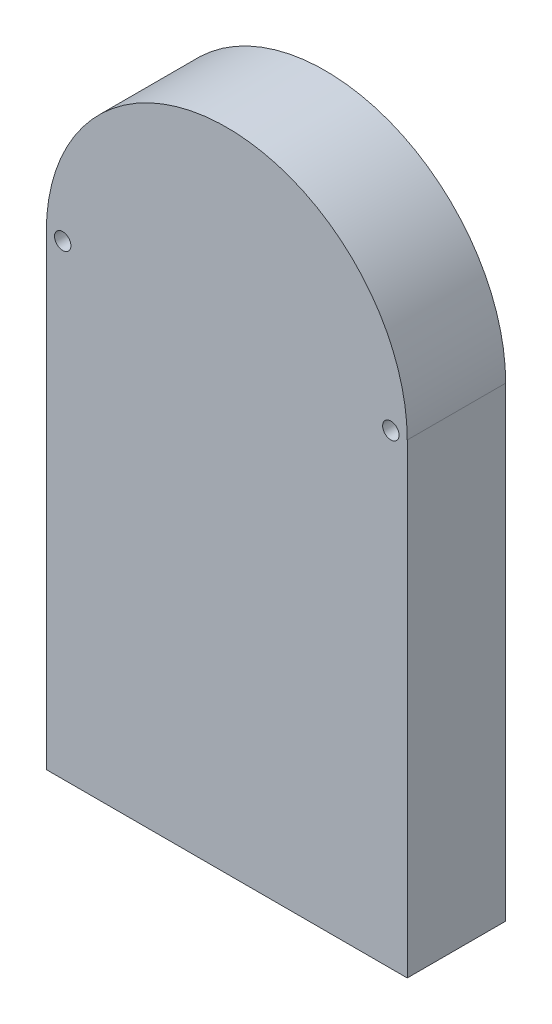
SolidWorks part; units mm, degrees
ref_plane "Front Plane" through (0, 0, 0) normal (0, 0, 1) x (1, 0, 0)
ref_plane "Top Plane" through (0, 0, 0) normal (0, 1, 0) x (1, 0, 0)
ref_plane "Right Plane" through (0, 0, 0) normal (1, 0, 0) x (0, 0, -1)
sketch "Sketch1" plane through (0, 0, 0) normal (0, 0, 1) x (1, 0, 0)
  line L0 (-57.2515, 0) -> (52.7485, 0)
  line L1 (52.7485, 0) -> (52.7485, 142)
  line L2 (-57.2515, 0) -> (-57.2515, 142)
  arc A0 (-57.2515, 142) -> (52.7485, 142) centre (-2.2515, 142) cw
  dimension "D1" = 110
  dimension "D2" = 142
  dimension "D3" = 142
extrude "Boss-Extrude1" add sketch "Sketch1" along normal blind 30
sketch "Sketch2" plane through (0, 0, 0) normal (0, 0, -1) x (-1, 0, 0)
  line L0 (-52.7485, 0) -> (57.2515, 0)
  line L1 (57.2515, 0) -> (57.2515, 142)
  line L2 (-52.7485, 0) -> (-52.7485, 142)
  line L7 (47.2515, 10) -> (47.2515, 142)
  line L8 (-42.7485, 10) -> (47.2515, 10)
  line L9 (-42.7485, 10) -> (-42.7485, 142)
  arc A4 (-52.7485, 142) -> (57.2515, 142) centre (2.2515, 142) cw
  arc A5 (-42.7485, 142) -> (47.2515, 142) centre (2.2515, 142) cw
  point P13 (47.2515, 150)
  dimension "D1" = 10
sketch "Sketch5" plane through (0, 0, 0) normal (0, -1, 0) x (-1, 0, 0)
  line L0 (57.2515, -30) -> (57.2515, 0) construction
  line L1 (-52.7485, -30) -> (-52.7485, 0) construction
  point P0 (42.2515, -15)
  point P1 (-37.7485, -15)
  dimension "D1" = 15
  dimension "D2" = 15
sketch "Sketch8" plane through (0, 0, 0) normal (0, 0, -1) x (-1, 0, 0)
  line L0 (-42.7485, 10) -> (47.2515, 10)
  line L1 (47.2515, 10) -> (47.2515, 142)
  line L2 (-42.7485, 10) -> (-42.7485, 142)
  arc A0 (-42.7485, 142) -> (47.2515, 142) centre (2.2515, 142) cw
extrude "Cut-Extrude1" cut sketch "Sketch8" against normal blind 25
hole_wizard "Ø5.0mm Dowel Hole2" positions "3DSketch2" profile "Sketch6" hole size "Ø5.0" standard "ANSI Metric"
sketch3d "3DSketch2"
  point P0 (-42.2515, 0, 15)
  point P3 (37.7485, 0, 15)
sketch "Sketch6" plane through (-42.2515, 0, 15) normal (1, 0, 0) x (0, 0, -1)
  line L0 (0, 0) -> (0, 11.5012)
  line L1 (0, 11.5012) -> (2.5, 9.999)
  line L2 (2.5, 9.999) -> (2.5, 0)
  line L5 (2.5, 0) -> (0, 0)
  line L10 (0, 11.5012) -> (-2.5, 9.999) construction
  line L11 (0, -6.35) -> (0, 107.95) construction
  dimension "Hole Dia." = 5
  dimension "Hole Depth" = 9.999
  dimension "Drill Angle" = 118
sketch "Sketch13" plane through (0, 0, 0) normal (0, 0, -1) x (-1, 0, 0)
  point P5 (52.2515, 142)
  point P6 (-47.7485, 142)
hole_wizard "Ø5.0mm Dowel Hole4" positions "3DSketch5" profile "Sketch14" hole size "Ø5.0" standard "ANSI Metric" end condition through all
sketch3d "3DSketch5"
  point P0 (47.7485, 142, 0)
  point P3 (-52.2515, 142, 0)
sketch "Sketch14" plane through (47.7485, 142, 0) normal (1, 0, 0) x (0, 1, 0)
  line L0 (0, 0) -> (0, 30)
  line L1 (0, 30) -> (2.5, 30)
  line L2 (2.5, 30) -> (2.5, 0)
  line L5 (2.5, 0) -> (0, 0)
  line L11 (0, -6.35) -> (0, 107.95) construction
  dimension "Thru Hole Dia." = 5
  dimension "Thru Hole Depth" = 30
